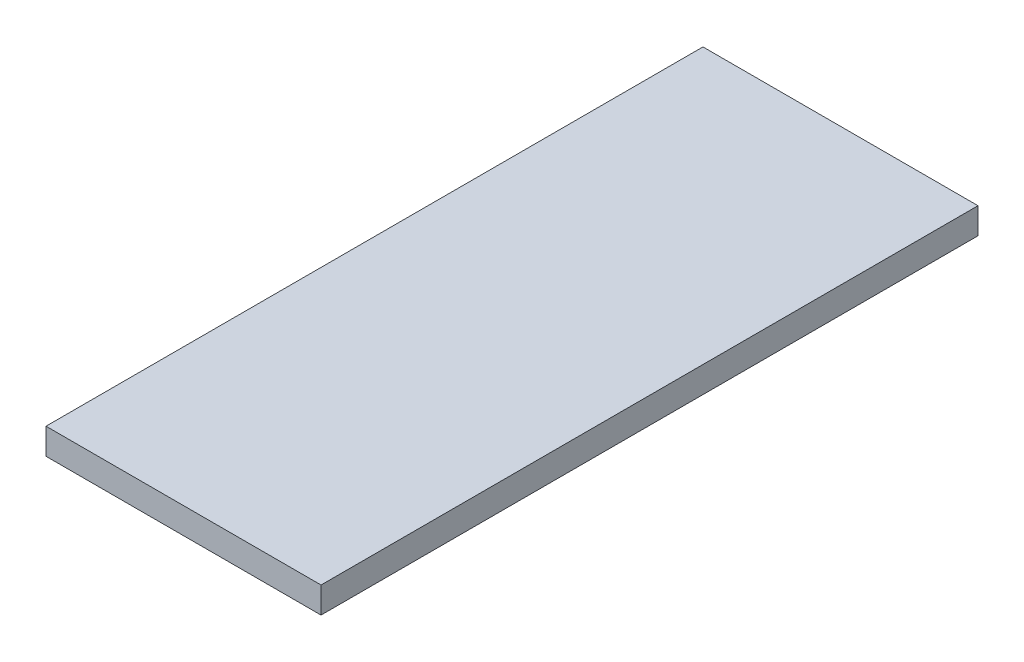
SolidWorks part; units mm, degrees
material "Oak"
ref_plane "Front Plane" through (0, 0, 0) normal (0, 0, 1) x (1, 0, 0)
ref_plane "Top Plane" through (0, 0, 0) normal (0, 1, 0) x (1, 0, 0)
ref_plane "Right Plane" through (0, 0, 0) normal (1, 0, 0) x (0, 0, -1)
sketch "Sketch1" plane through (0, 0, 0) normal (0, 1, 0) x (1, 0, 0)
  line L1 (0, 0) -> (50.24, 0)
  line L2 (0, 0) -> (0, 120)
  line L3 (0, 120) -> (50.24, 120)
  line L4 (50.24, 0) -> (50.24, 120)
  dimension "D1" = 120
  dimension "D2" = 50.24
extrude "Boss-Extrude1" add sketch "Sketch1" along normal blind 4.7625
